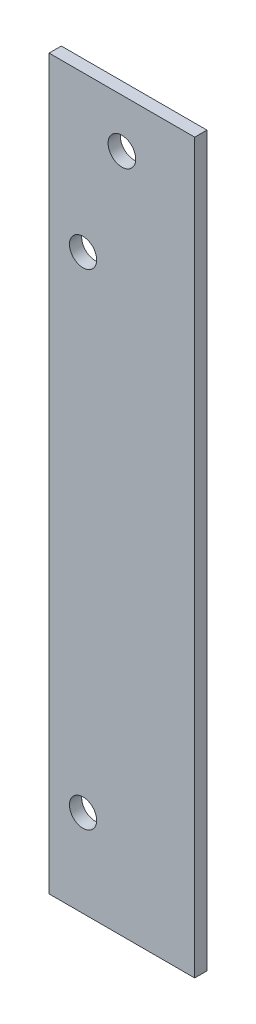
SolidWorks part; units mm, degrees
ref_plane "Front" through (0, 0, 0) normal (0, 0, 1) x (1, 0, 0)
ref_plane "Top" through (0, 0, 0) normal (0, 1, 0) x (1, 0, 0)
ref_plane "Right" through (0, 0, 0) normal (1, 0, 0) x (0, 0, -1)
sketch "Sketch1" plane through (0, 0, 0) normal (0, 0, 1) x (1, 0, 0)
  line L1 (0, 0) -> (19.05, 0)
  line L2 (0, 0) -> (0, -95.25)
  line L3 (0, -95.25) -> (19.05, -95.25)
  line L4 (19.05, 0) -> (19.05, -95.25)
  dimension "D1" = 19.05
  dimension "D2" = 95.25
extrude "Extrude1" add sketch "Sketch1" along normal blind 1.6002
sketch "Sketch2" plane through (0, 0, 1.6002) normal (0, 0, 1) x (1, 0, 0)
  line L0 (19.05, -95.25) -> (19.05, 0) construction
  line L1 (19.05, 0) -> (0, 0) construction
  circle A0 centre (9.525, -6.35) radius 1.8034
  dimension "D1" = 3.6068
  dimension "D3" = 9.525
  dimension "D4" = 6.35
extrude "Cut-Extrude1" cut sketch "Sketch2" against normal blind 1.6002
sketch "Sketch3" plane through (0, 0, 1.6002) normal (0, 0, 1) x (1, 0, 0)
  line L0 (0, -95.25) -> (19.05, -95.25) construction
  line L2 (0, 0) -> (0, -95.25) construction
  circle A0 centre (4.445, -20.32) radius 1.778
  circle A1 centre (4.445, -83.82) radius 1.778
  dimension "D1" = 3.556
  dimension "D2" = 3.556
  dimension "D3" = 11.43
  dimension "D4" = 4.445
  dimension "D5" = 63.5
extrude "Cut-Extrude2" cut sketch "Sketch3" against normal blind 2.54
